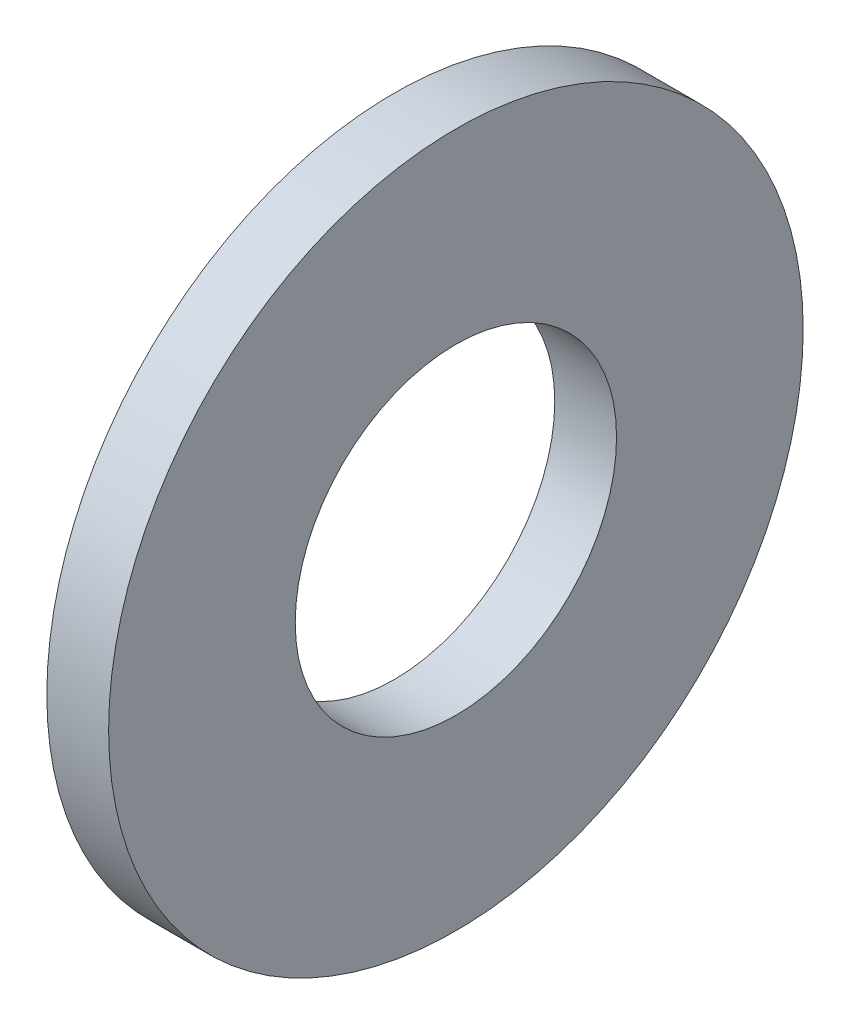
SolidWorks part; units mm, degrees
ref_plane "Front Plane" through (0, 0, 0) normal (0, 0, 1) x (1, 0, 0)
ref_plane "Top Plane" through (0, 0, 0) normal (0, 1, 0) x (1, 0, 0)
ref_plane "Right Plane" through (0, 0, 0) normal (1, 0, 0) x (0, 0, -1)
sketch "Sketch1" plane through (0, 0, 0) normal (1, 0, 0) x (0, 0, -1)
  circle A0 centre (0, 0) radius 7.1374
  circle A1 centre (0, 0) radius 3.302
  dimension "OD" = 14.2748
  dimension "ID" = 6.604
extrude "Boss-Extrude1" add sketch "Sketch1" along normal blind 1.27
